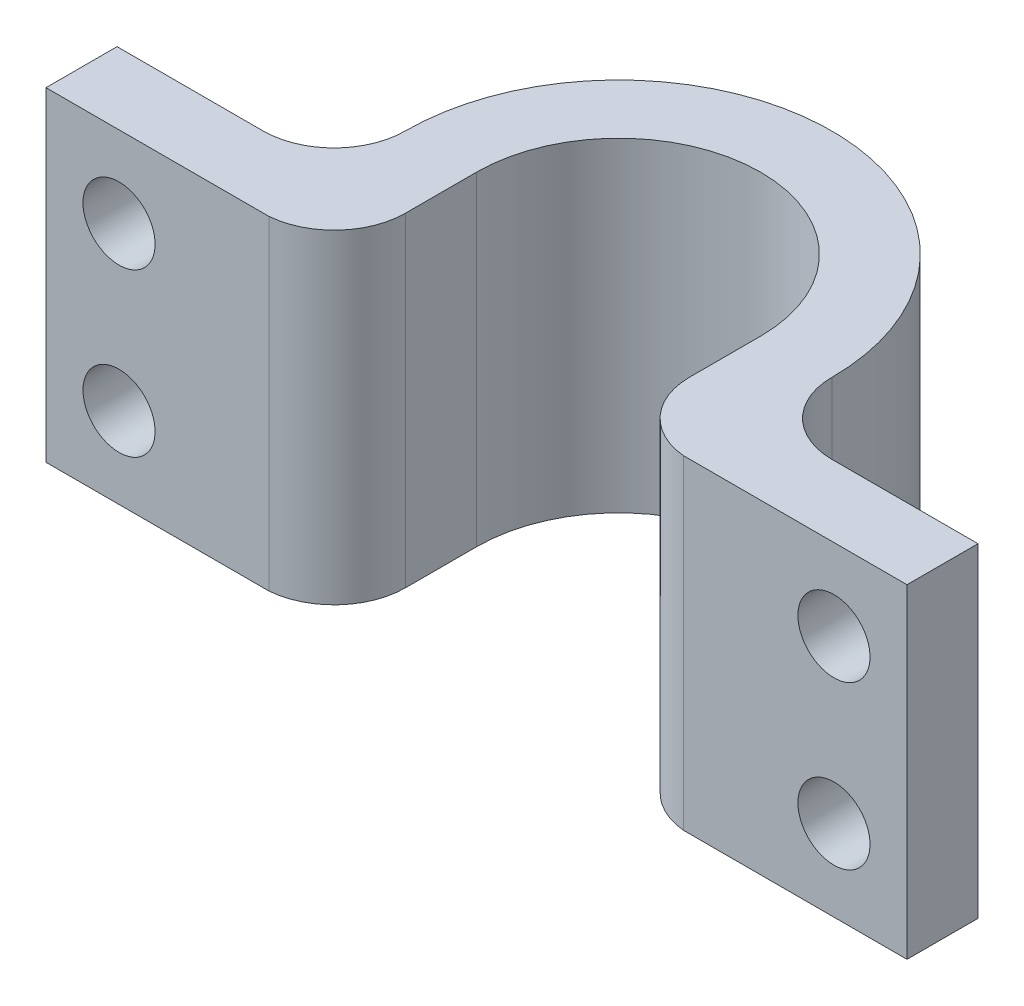
SolidWorks part; units mm, degrees
ref_plane "Ön Düzlem" through (0, 0, 0) normal (0, 0, 1) x (1, 0, 0)
ref_plane "Üst Düzlem" through (0, 0, 0) normal (0, 1, 0) x (1, 0, 0)
ref_plane "Sağ Düzlem" through (0, 0, 0) normal (1, 0, 0) x (0, 0, -1)
sketch "Çizim1" plane through (0, 0, 0) normal (0, 1, 0) x (1, 0, 0)
  line L0 (3.94, 0) -> (3.94, -1.9708)
  line L1 (-3.94, 0) -> (-3.94, -1.9708)
  line L2 (-5.7529, -3.9416) -> (-11.94, -3.9416)
  line L3 (5.7347, -3.94) -> (11.94, -3.94)
  line L4 (-11.94, -3.9416) -> (-11.94, -1.9708)
  line L5 (0, 6.5932) -> (0, 3.94) construction
  line L6 (-11.94, -1.9708) -> (-7.8885, -1.9708)
  line L8 (11.94, -3.94) -> (11.94, -1.9708)
  line L9 (11.94, -1.9708) -> (7.8885, -1.9708)
  arc A0 (3.94, 0) -> (-3.94, 0) centre (0, 0) ccw
  arc A1 (-3.94, -1.9708) -> (-5.7529, -3.9416) centre (-5.9177, -1.9708) cw
  arc A2 (3.94, -1.9708) -> (5.7347, -3.94) centre (5.9177, -1.9708) ccw
  arc A3 (5.9177, 0) -> (-5.9177, 0) centre (0, 0) ccw
  arc A4 (5.9177, 0) -> (7.8885, -1.9708) centre (7.8885, 0) ccw
  arc A5 (-5.9177, 0) -> (-7.8885, -1.9708) centre (-7.8885, 0) cw
  dimension "D1" = 7.88
extrude "Yükseklik-Ekstrüzyon1" add sketch "Çizim1" along normal blind 9
sketch "Çizim2" plane through (0, 0, 1.9708) normal (0, 0, -1) x (-1, 0, 0)
  line L0 (-9.9142, 9) -> (-9.9142, 0) construction
  line L1 (-11.94, 9) -> (-7.8885, 9) construction
  line L2 (-11.94, 0) -> (-7.8885, 0) construction
  line L3 (-11.94, 9) -> (-11.94, 4.5) construction
  line L4 (-11.94, 9) -> (-11.94, 0) construction
  line L5 (-11.94, 4.5) -> (-11.94, 0) construction
  line L6 (0, 11.1426) -> (0, -1.0983) construction
  line L7 (9.9142, 9) -> (9.9142, 0) construction
  circle A0 centre (-9.9142, 6.75) radius 1
  circle A1 centre (-9.9142, 2.25) radius 1
  circle A2 centre (9.9142, 2.25) radius 1
  circle A3 centre (9.9142, 6.75) radius 1
  dimension "D1" = 2
  dimension "D2" = 2
extrude "Kes-Ekstrüzyon1" cut sketch "Çizim2" against normal blind 9
scale "Ölçek1" scale about centroid uniform scaling yes scale factor 0.5
